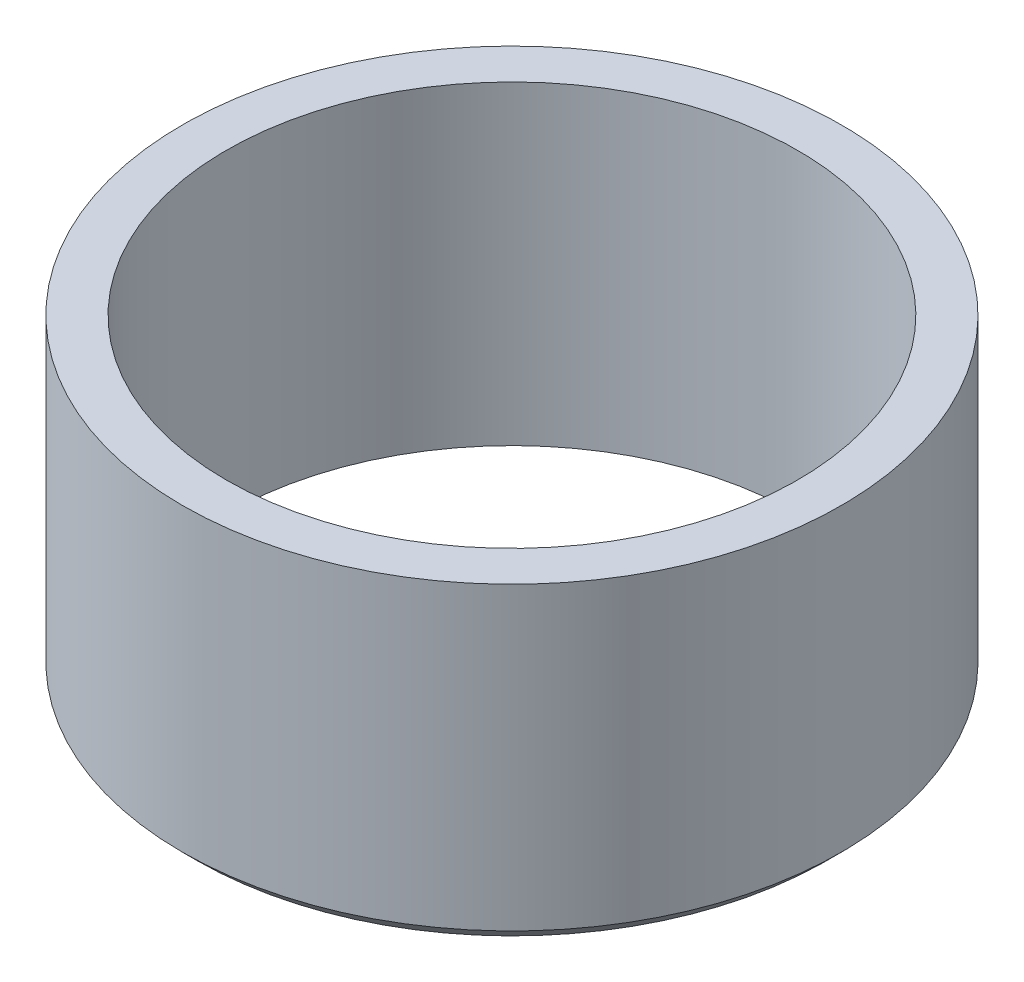
SolidWorks part; units mm, degrees
ref_plane "Front Plane" through (0, 0, 0) normal (0, 0, 1) x (1, 0, 0)
ref_plane "Top Plane" through (0, 0, 0) normal (0, 1, 0) x (1, 0, 0)
ref_plane "Right Plane" through (0, 0, 0) normal (1, 0, 0) x (0, 0, -1)
sketch "Sketch1" plane through (0, 0, 0) normal (0, 1, 0) x (1, 0, 0)
  circle A0 centre (0, 0) radius 4.5
  dimension "D1" = 9
extrude "Boss-Extrude1" add sketch "Sketch1" along normal blind 4.3
sketch "Sketch2" plane through (0, 4.3, 0) normal (0, 1, 0) x (1, 0, 0)
  circle A0 centre (0, 0) radius 3.9
  dimension "D1" = 7.8
extrude "Cut-Extrude1" cut sketch "Sketch2" against normal through all
chamfer "Chamfer1" distance 0.2 angle 45 1 edges at (0, 0, 4.5)
